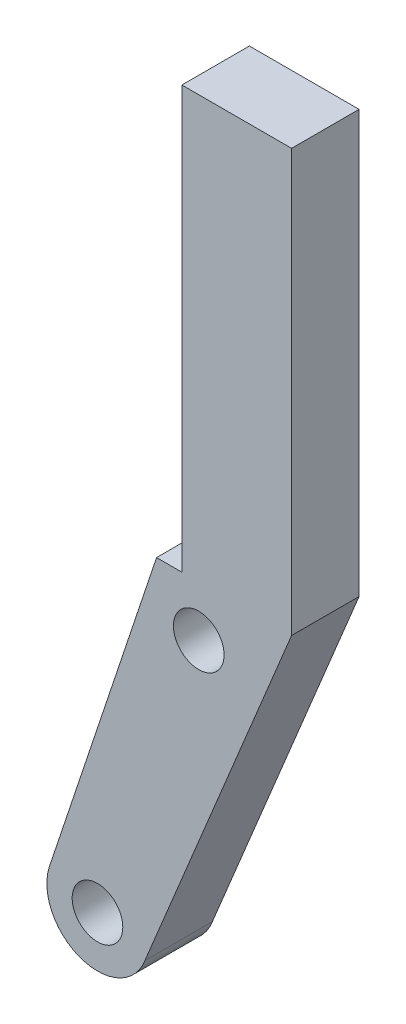
SolidWorks part; units mm, degrees
material "Beech"
ref_plane "Front Plane" through (0, 0, 0) normal (0, 0, 1) x (1, 0, 0)
ref_plane "Top Plane" through (0, 0, 0) normal (0, 1, 0) x (1, 0, 0)
ref_plane "Right Plane" through (0, 0, 0) normal (1, 0, 0) x (0, 0, -1)
sketch "Sketch1" plane through (0, 0, 0) normal (0, 0, 1) x (1, 0, 0)
  line L0 (14.4885, 22.9654) -> (14.4885, 47.9654)
  line L1 (14.4885, 47.9654) -> (7.9885, 47.9654)
  line L2 (7.9885, 47.9654) -> (7.9885, 22.9654)
  line L3 (7.9885, 22.9654) -> (6.4885, 22.9654)
  line L4 (0.12, 3.8738) -> (6.4885, 22.9654)
  line L5 (5.7949, 1.935) -> (14.4885, 22.9654)
  circle A0 centre (2.9885, 2.9954) radius 1.5
  circle A1 centre (8.9885, 19.9654) radius 1.5
  arc A2 (0.12, 3.8738) -> (5.7949, 1.935) centre (2.9885, 2.9954) ccw
extrude "Boss-Extrude1" add sketch "Sketch1" along normal blind 4
